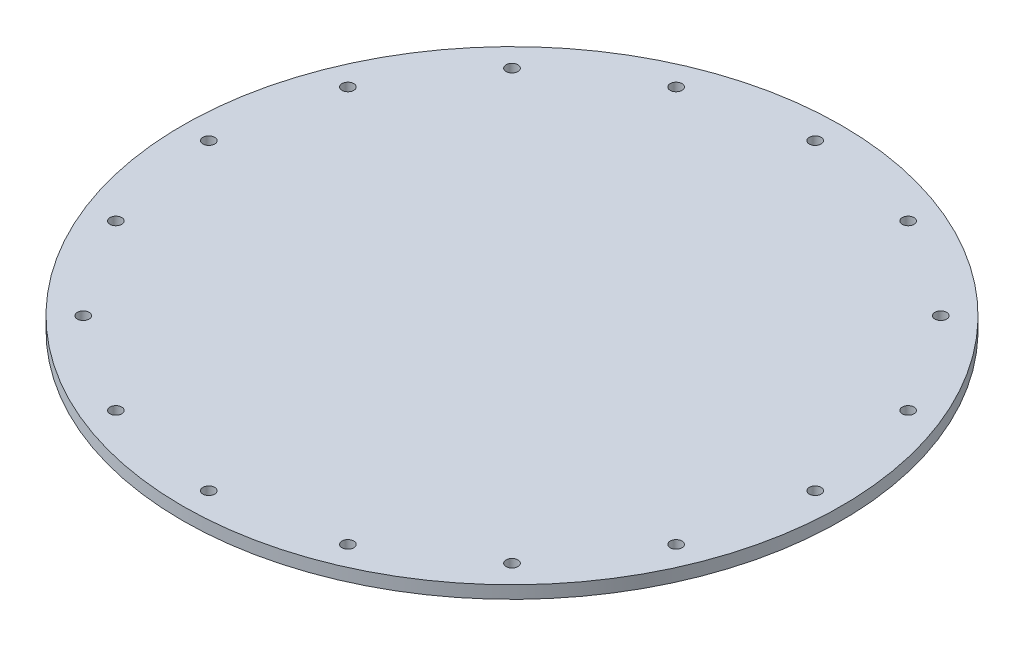
SolidWorks part; units mm, degrees
ref_plane "Front" through (0, 0, 0) normal (0, 0, 1) x (1, 0, 0)
ref_plane "Top" through (0, 0, 0) normal (0, 1, 0) x (1, 0, 0)
ref_plane "Right" through (0, 0, 0) normal (1, 0, 0) x (0, 0, -1)
sketch "Sketch1" plane through (0, 0, 0) normal (0, 1, 0) x (1, 0, 0)
  circle A0 centre (0, 0) radius 79.375
  circle A1 centre (0, 0) radius 73.025 construction
  circle A2 centre (0, 73.025) radius 1.4224
  circle A3 centre (27.9455, 67.4663) radius 1.4224
  circle A4 centre (51.6365, 51.6365) radius 1.4224
  circle A5 centre (67.4663, 27.9455) radius 1.4224
  circle A6 centre (73.025, 0) radius 1.4224
  circle A7 centre (67.4663, -27.9455) radius 1.4224
  circle A8 centre (51.6365, -51.6365) radius 1.4224
  circle A9 centre (27.9455, -67.4663) radius 1.4224
  circle A10 centre (0, -73.025) radius 1.4224
  circle A11 centre (-27.9455, -67.4663) radius 1.4224
  circle A12 centre (-51.6365, -51.6365) radius 1.4224
  circle A13 centre (-67.4663, -27.9455) radius 1.4224
  circle A14 centre (-73.025, 0) radius 1.4224
  circle A15 centre (-67.4663, 27.9455) radius 1.4224
  circle A16 centre (-51.6365, 51.6365) radius 1.4224
  circle A17 centre (-27.9455, 67.4663) radius 1.4224
  point P38 (0, 0)
  dimension "D1" = 158.75
  dimension "D2" = 2.8448
  dimension "D3" = 146.05
  dimension "D4" = 16
extrude "Boss-Extrude1" add sketch "Sketch1" along normal blind 3.048
